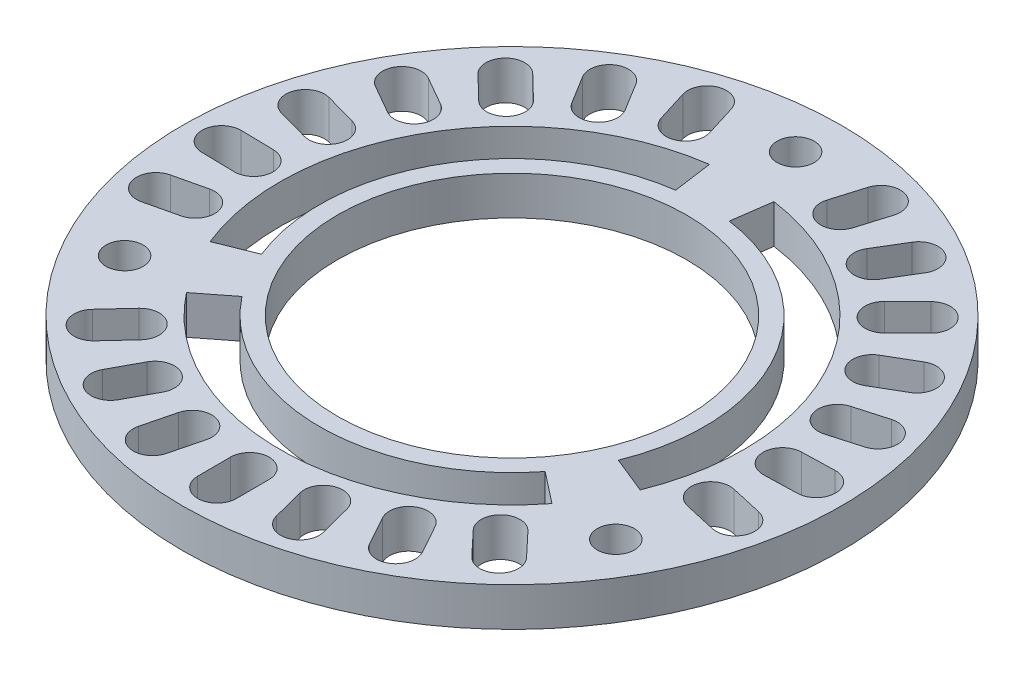
SolidWorks part; units mm, degrees
ref_plane "Front Plane" through (0, 0, 0) normal (0, 0, 1) x (1, 0, 0)
ref_plane "Top Plane" through (0, 0, 0) normal (0, 1, 0) x (1, 0, 0)
ref_plane "Right Plane" through (0, 0, 0) normal (1, 0, 0) x (0, 0, -1)
sketch "Sketch1" plane through (0, 0, 0) normal (0, 1, 0) x (1, 0, 0)
  line L211 (-126.2276, 73.4215) -> (-126.2276, 95.0115) construction
  line L212 (-126.2276, 73.4215) -> (-107.5301, 62.6265) construction
  line L213 (-126.2276, 73.4215) -> (-144.9251, 62.6265) construction
  line L214 (-126.2276, 73.4215) -> (-124.1129, 88.4686) construction
  line L215 (-124.1129, 88.4686) -> (-124.4737, 85.9012)
  line L216 (-126.2276, 73.4215) -> (-112.139, 67.7293) construction
  line L217 (-112.139, 67.7293) -> (-114.5429, 68.7005)
  line L218 (-126.2276, 73.4215) -> (-120.633, 92.0012) construction
  line L219 (-120.633, 92.0012) -> (-121.2529, 89.9423) construction
  line L220 (-119.4187, 91.6355) -> (-120.0387, 89.5767)
  line L221 (-121.8472, 92.3668) -> (-122.4672, 90.3079)
  line L222 (-116.2075, 90.0378) -> (-117.3179, 88.1965) construction
  line L223 (-115.1216, 89.3829) -> (-116.2319, 87.5416)
  line L224 (-117.2934, 90.6926) -> (-118.4038, 88.8513)
  line L225 (-112.4058, 87.04) -> (-113.9375, 85.5309) construction
  line L226 (-111.5158, 86.1367) -> (-113.0474, 84.6276)
  line L227 (-113.2958, 87.9433) -> (-114.8275, 86.4342)
  line L228 (-109.4646, 83.1943) -> (-111.3222, 82.1113) construction
  line L229 (-108.826, 82.0988) -> (-110.6835, 81.0158)
  line L230 (-110.1033, 84.2898) -> (-111.9609, 83.2068)
  line L231 (-107.5671, 78.7402) -> (-109.6349, 78.1508) construction
  line L232 (-107.2195, 77.5207) -> (-109.2873, 76.9313)
  line L233 (-107.9147, 79.9597) -> (-109.9825, 79.3703)
  line L234 (-106.8312, 73.955) -> (-108.9806, 73.8959) construction
  line L235 (-106.7963, 72.6874) -> (-108.9457, 72.6283)
  line L236 (-106.8661, 75.2226) -> (-109.0155, 75.1635)
  line L237 (-107.3029, 69.1366) -> (-109.4, 69.6114) construction
  line L238 (-107.5829, 67.8998) -> (-109.68, 68.3746)
  line L239 (-107.0229, 70.3734) -> (-109.12, 70.8482)
  line L240 (-138.2014, 64.0665) -> (-136.1584, 65.6627)
  line L241 (-114.2537, 64.0665) -> (-116.2968, 65.6627)
  line L242 (-112.9344, 59.2866) -> (-114.4075, 60.8529) construction
  line L243 (-113.8582, 58.4178) -> (-115.3312, 59.9842)
  line L244 (-112.0107, 60.1553) -> (-113.4837, 61.7217)
  line L245 (-116.8475, 56.4357) -> (-117.8869, 58.3179) construction
  line L246 (-117.9576, 55.8227) -> (-118.997, 57.7049)
  line L247 (-115.7374, 57.0487) -> (-116.7768, 58.9309)
  line L248 (-121.3445, 54.6422) -> (-121.8856, 56.7232) construction
  line L249 (-122.5718, 54.3231) -> (-123.1129, 56.4041)
  line L250 (-120.1172, 54.9614) -> (-120.6583, 57.0424)
  line L251 (-126.1456, 54.0179) -> (-126.1547, 56.1681) construction
  line L252 (-127.4136, 54.0126) -> (-127.4227, 56.1627)
  line L253 (-124.8775, 54.0233) -> (-124.8866, 56.1735)
  line L254 (-130.9517, 54.6016) -> (-130.4282, 56.6871) construction
  line L255 (-132.1816, 54.9104) -> (-131.6582, 56.9959)
  line L256 (-129.7218, 54.2929) -> (-129.1983, 56.3784)
  line L257 (-135.4637, 56.357) -> (-134.4403, 58.2479) construction
  line L258 (-136.579, 56.9606) -> (-135.5555, 58.8516)
  line L259 (-134.3485, 55.7534) -> (-133.325, 57.6443)
  line L260 (-139.4008, 59.1747) -> (-137.941, 60.7534) construction
  line L261 (-140.3319, 60.0356) -> (-138.8721, 61.6143)
  line L262 (-138.4697, 58.3138) -> (-137.0099, 59.8925)
  line L263 (-128.3423, 88.4686) -> (-127.9815, 85.9012)
  line L264 (-140.3162, 67.7293) -> (-137.9123, 68.7005)
  line L265 (-145.1154, 68.9767) -> (-143.0224, 69.4692) construction
  line L266 (-145.4058, 70.2111) -> (-143.3128, 70.7036)
  line L267 (-144.8249, 67.7423) -> (-142.7319, 68.2349)
  line L268 (-145.6278, 73.791) -> (-143.478, 73.75) construction
  line L269 (-145.6036, 75.0588) -> (-143.4538, 75.0179)
  line L270 (-145.6519, 72.5231) -> (-143.5021, 72.4822)
  line L271 (-144.9324, 78.5822) -> (-142.8597, 78.0104) construction
  line L272 (-144.5951, 79.8047) -> (-142.5224, 79.2328)
  line L273 (-145.2697, 77.3598) -> (-143.197, 76.7879)
  line L274 (-143.0726, 83.0522) -> (-141.2059, 81.985) construction
  line L275 (-142.4432, 84.1531) -> (-140.5765, 83.0859)
  line L276 (-143.702, 81.9513) -> (-141.8353, 80.8841)
  line L277 (-140.164, 86.9226) -> (-138.6197, 85.4265) construction
  line L278 (-139.2817, 87.8334) -> (-137.7373, 86.3373)
  line L279 (-141.0463, 86.0118) -> (-139.502, 84.5157)
  line L280 (-136.3878, 89.9525) -> (-135.2619, 88.1206) construction
  line L281 (-135.3075, 90.6165) -> (-134.1816, 88.7846)
  line L282 (-137.4682, 89.2885) -> (-136.3423, 87.4566)
  line L283 (-131.9791, 91.9532) -> (-131.3417, 89.8996) construction
  line L284 (-130.768, 92.3291) -> (-130.1306, 90.2755)
  line L285 (-133.1902, 91.5773) -> (-132.5528, 89.5238)
  circle A93 centre (-126.2276, 73.4215) radius 21.59
  circle A94 centre (-126.2276, 73.4215) radius 11.43
  arc A95 (-124.4737, 85.9012) -> (-114.5429, 68.7005) centre (-126.2276, 73.4215) cw
  arc A96 (-112.139, 67.7293) -> (-124.1129, 88.4686) centre (-126.2276, 73.4215) ccw
  arc A97 (-119.4187, 91.6355) -> (-121.8472, 92.3668) centre (-120.633, 92.0012) ccw
  arc A98 (-122.4672, 90.3079) -> (-120.0387, 89.5767) centre (-121.2529, 89.9423) ccw
  arc A99 (-115.1216, 89.3829) -> (-117.2934, 90.6926) centre (-116.2075, 90.0378) ccw
  arc A100 (-118.4038, 88.8513) -> (-116.2319, 87.5416) centre (-117.3179, 88.1965) ccw
  arc A101 (-111.5158, 86.1367) -> (-113.2958, 87.9433) centre (-112.4058, 87.04) ccw
  arc A102 (-114.8275, 86.4342) -> (-113.0474, 84.6276) centre (-113.9375, 85.5309) ccw
  arc A103 (-108.826, 82.0988) -> (-110.1033, 84.2898) centre (-109.4646, 83.1943) ccw
  arc A104 (-111.9609, 83.2068) -> (-110.6835, 81.0158) centre (-111.3222, 82.1113) ccw
  arc A105 (-107.2195, 77.5207) -> (-107.9147, 79.9597) centre (-107.5671, 78.7402) ccw
  arc A106 (-109.9825, 79.3703) -> (-109.2873, 76.9313) centre (-109.6349, 78.1508) ccw
  arc A107 (-106.7963, 72.6874) -> (-106.8661, 75.2226) centre (-106.8312, 73.955) ccw
  arc A108 (-109.0155, 75.1635) -> (-108.9457, 72.6283) centre (-108.9806, 73.8959) ccw
  arc A109 (-107.5829, 67.8998) -> (-107.0229, 70.3734) centre (-107.3029, 69.1366) ccw
  arc A110 (-109.12, 70.8482) -> (-109.68, 68.3746) centre (-109.4, 69.6114) ccw
  circle A111 centre (-126.2276, 92.0012) radius 1.2173
  circle A112 centre (-110.1371, 64.1316) radius 1.2173
  arc A113 (-138.2014, 64.0665) -> (-114.2537, 64.0665) centre (-126.2276, 73.4215) ccw
  arc A114 (-116.2968, 65.6627) -> (-136.1584, 65.6627) centre (-126.2276, 73.4215) cw
  arc A115 (-113.8582, 58.4178) -> (-112.0107, 60.1553) centre (-112.9344, 59.2866) ccw
  arc A116 (-113.4837, 61.7217) -> (-115.3312, 59.9842) centre (-114.4075, 60.8529) ccw
  arc A117 (-117.9576, 55.8227) -> (-115.7374, 57.0487) centre (-116.8475, 56.4357) ccw
  arc A118 (-116.7768, 58.9309) -> (-118.997, 57.7049) centre (-117.8869, 58.3179) ccw
  arc A119 (-122.5718, 54.3231) -> (-120.1172, 54.9614) centre (-121.3445, 54.6422) ccw
  arc A120 (-120.6583, 57.0424) -> (-123.1129, 56.4041) centre (-121.8856, 56.7232) ccw
  arc A121 (-127.4136, 54.0126) -> (-124.8775, 54.0233) centre (-126.1456, 54.0179) ccw
  arc A122 (-124.8866, 56.1735) -> (-127.4227, 56.1627) centre (-126.1547, 56.1681) ccw
  arc A123 (-132.1816, 54.9104) -> (-129.7218, 54.2929) centre (-130.9517, 54.6016) ccw
  arc A124 (-129.1983, 56.3784) -> (-131.6582, 56.9959) centre (-130.4282, 56.6871) ccw
  arc A125 (-136.579, 56.9606) -> (-134.3485, 55.7534) centre (-135.4637, 56.357) ccw
  arc A126 (-133.325, 57.6443) -> (-135.5555, 58.8516) centre (-134.4403, 58.2479) ccw
  arc A127 (-140.3319, 60.0356) -> (-138.4697, 58.3138) centre (-139.4008, 59.1747) ccw
  arc A128 (-137.0099, 59.8925) -> (-138.8721, 61.6143) centre (-137.941, 60.7534) ccw
  circle A129 centre (-142.3181, 64.1316) radius 1.2173
  arc A130 (-128.3423, 88.4686) -> (-140.3162, 67.7293) centre (-126.2276, 73.4215) ccw
  arc A131 (-137.9123, 68.7005) -> (-127.9815, 85.9012) centre (-126.2276, 73.4215) cw
  arc A132 (-145.4058, 70.2111) -> (-144.8249, 67.7423) centre (-145.1154, 68.9767) ccw
  arc A133 (-142.7319, 68.2349) -> (-143.3128, 70.7036) centre (-143.0224, 69.4692) ccw
  arc A134 (-145.6036, 75.0588) -> (-145.6519, 72.5231) centre (-145.6278, 73.791) ccw
  arc A135 (-143.5021, 72.4822) -> (-143.4538, 75.0179) centre (-143.478, 73.75) ccw
  arc A136 (-144.5951, 79.8047) -> (-145.2697, 77.3598) centre (-144.9324, 78.5822) ccw
  arc A137 (-143.197, 76.7879) -> (-142.5224, 79.2328) centre (-142.8597, 78.0104) ccw
  arc A138 (-142.4432, 84.1531) -> (-143.702, 81.9513) centre (-143.0726, 83.0522) ccw
  arc A139 (-141.8353, 80.8841) -> (-140.5765, 83.0859) centre (-141.2059, 81.985) ccw
  arc A140 (-139.2817, 87.8334) -> (-141.0463, 86.0118) centre (-140.164, 86.9226) ccw
  arc A141 (-139.502, 84.5157) -> (-137.7373, 86.3373) centre (-138.6197, 85.4265) ccw
  arc A142 (-135.3075, 90.6165) -> (-137.4682, 89.2885) centre (-136.3878, 89.9525) ccw
  arc A143 (-136.3423, 87.4566) -> (-134.1816, 88.7846) centre (-135.2619, 88.1206) ccw
  arc A144 (-130.768, 92.3291) -> (-133.1902, 91.5773) centre (-131.9791, 91.9532) ccw
  arc A145 (-132.5528, 89.5238) -> (-130.1306, 90.2755) centre (-131.3417, 89.8996) ccw
  point P396 (-120.943, 90.9717)
  point P397 (-116.7627, 89.1171)
  point P414 (-113.1716, 86.2854)
  point P421 (-110.3934, 82.6528)
  point P428 (-108.601, 78.4455)
  point P435 (-107.9059, 73.9254)
  point P442 (-108.3515, 69.374)
  point P449 (-126.2276, 73.4215)
  point P452 (-113.6709, 60.0697)
  point P453 (-117.3672, 57.3768)
  point P470 (-121.6151, 55.6827)
  point P477 (-126.1501, 55.093)
  point P484 (-130.69, 55.6444)
  point P491 (-134.952, 57.3025)
  point P498 (-138.6709, 59.9641)
  point P507 (-144.0689, 69.223)
  point P508 (-144.5529, 73.7705)
  point P525 (-143.896, 78.2963)
  point P532 (-142.1392, 82.5186)
  point P539 (-139.3918, 86.1746)
  point P546 (-135.8249, 89.0366)
  point P553 (-131.6604, 90.9264)
  point P560 (-126.2276, 73.4215)
  dimension "D33" = 120
  dimension "D34" = 120
  dimension "D35" = 8
  dimension "D36" = 8
  dimension "D37" = 17.2535
extrude "Boss-Extrude1" add sketch "Sketch1" along normal blind 2.54
